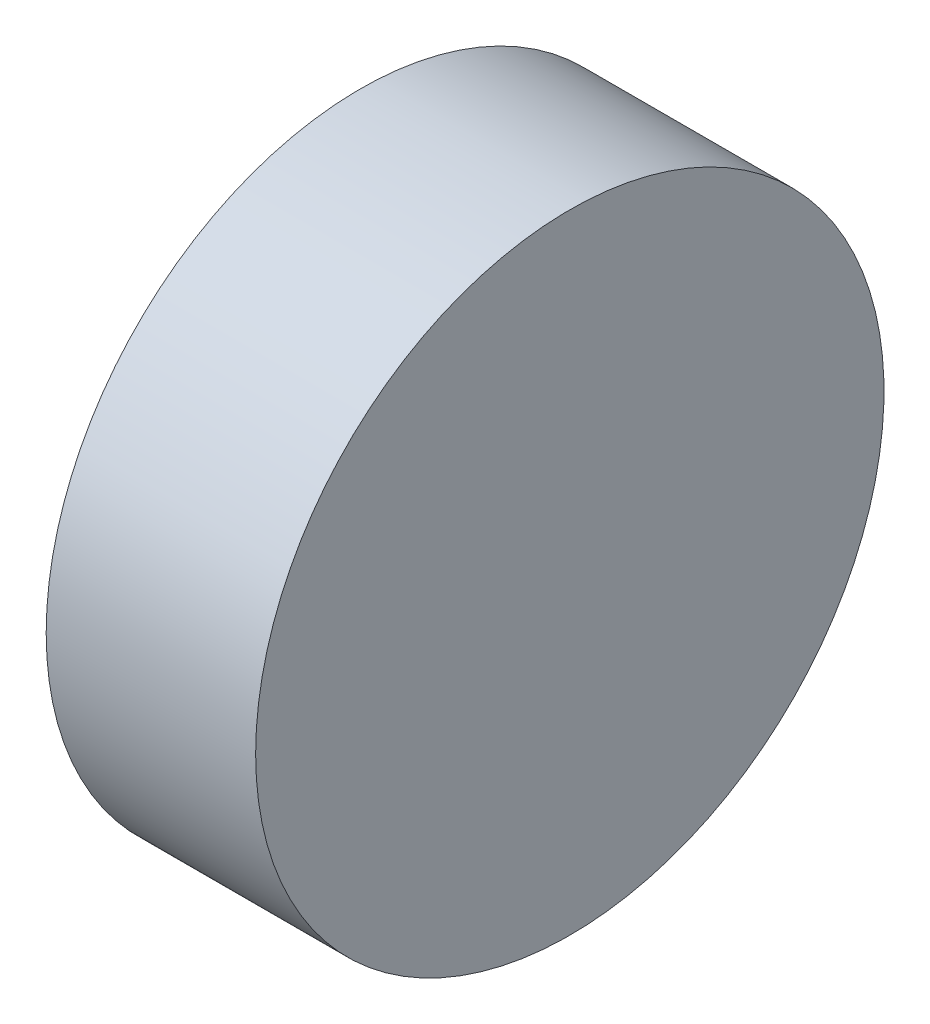
SolidWorks part; units mm, degrees
ref_plane "前视基准面" through (0, 0, 0) normal (0, 0, 1) x (1, 0, 0)
ref_plane "上视基准面" through (0, 0, 0) normal (0, 1, 0) x (1, 0, 0)
ref_plane "右视基准面" through (0, 0, 0) normal (1, 0, 0) x (0, 0, -1)
sketch "草图1" plane through (0, 0, 0) normal (0, 0, 1) x (1, 0, 0)
  line L0 (254.0008, 77.2932) -> (276.8371, 77.2932) construction
  line L1 (260.1163, 77.2932) -> (260.1163, 92.2932)
  line L2 (270.1163, 77.2932) -> (270.1163, 92.2932)
  line L3 (260.1163, 77.2932) -> (270.1163, 77.2932)
  line L5 (260.1163, 92.2932) -> (270.1163, 92.2932)
  dimension "D1" = 10
  dimension "D2" = 15
revolve "旋转1" add sketch "草图1" angle 360 about L0
